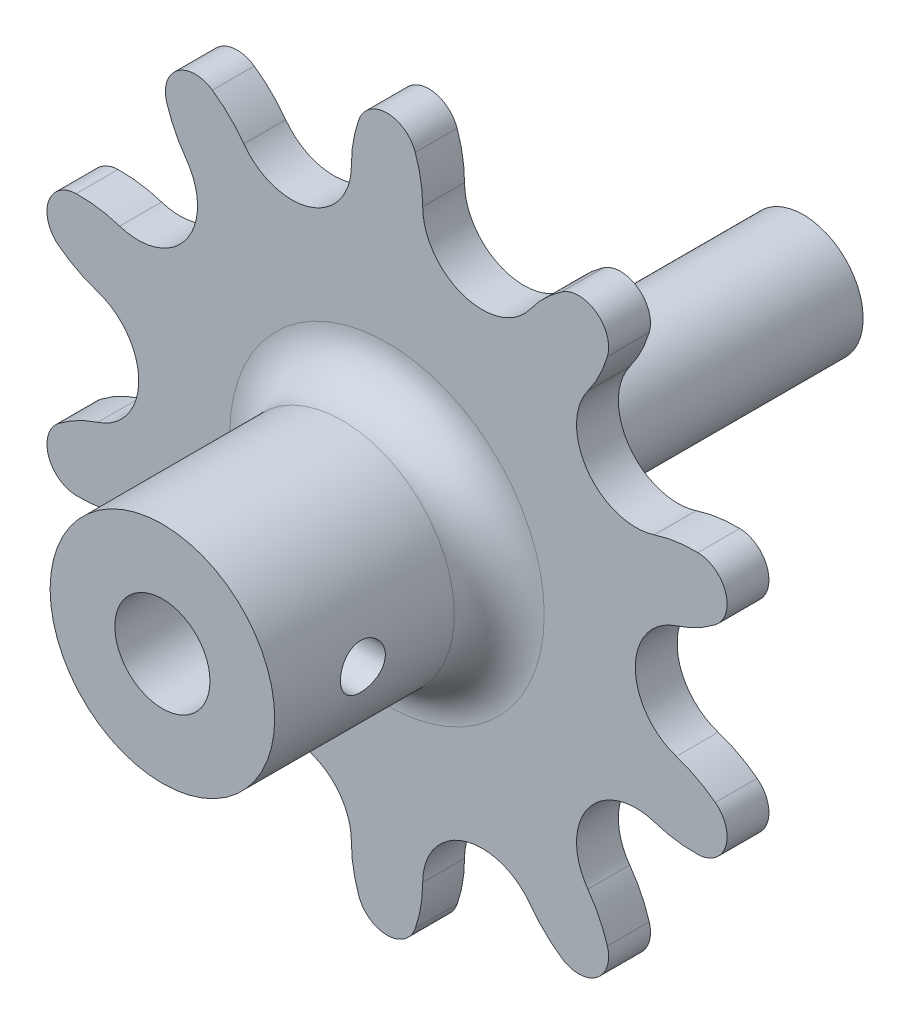
SolidWorks part; units mm, degrees
ref_plane "Front Plane" through (0, 0, 0) normal (0, 0, 1) x (1, 0, 0)
ref_plane "Top Plane" through (0, 0, 0) normal (0, 1, 0) x (1, 0, 0)
ref_plane "Right Plane" through (0, 0, 0) normal (1, 0, 0) x (0, 0, -1)
sketch "Sketch2" plane through (0, 0, 0) normal (0, 0, 1) x (1, 0, 0)
  line L0 (0, 0) -> (-12.7, 0) construction
  line L1 (-6.35, 0) -> (-6.35, -19.5433) construction
  line L2 (-6.35, -19.5433) -> (-12.7, 0) construction
  line L3 (-6.35, -19.5433) -> (0, 0) construction
  line L4 (-6.35, 0) -> (-6.35, 13.4382) construction
  circle A0 centre (0, 0) radius 3.9688 construction
  circle A1 centre (-12.7, 0) radius 3.9688 construction
  arc A2 (-8.7312, 0) -> (-8.2367, 2.8967) centre (0, 0) cw
  arc A3 (-3.9688, 0) -> (-4.4633, 2.8967) centre (-12.7, 0) ccw
  arc A4 (-8.2367, 2.8967) -> (-4.4633, 2.8967) centre (-6.35, 2.2332) cw
  arc A5 (-8.7312, 0) -> (-11.4736, -3.7745) centre (-12.7, 0) cw
  arc A6 (-3.9688, 0) -> (-1.2264, -3.7745) centre (0, 0) ccw
  arc A7 (3.2108, -2.3328) -> (-1.2264, -3.7745) centre (0, 0) cw
  arc A8 (7.0637, -5.1321) -> (7.0637, -9.7976) centre (10.2745, -7.4649) ccw
  arc A9 (7.0637, -5.1321) -> (8.3663, -2.4979) centre (0, 0) ccw
  arc A10 (5.3135, -0.2799) -> (8.3663, -2.4979) centre (6.4499, -1.9257) cw
  arc A11 (3.2108, -2.3328) -> (5.3135, -0.2799) centre (10.2745, -7.4649) cw
  arc A12 (11.5009, -11.2394) -> (7.0637, -9.7976) centre (10.2745, -7.4649) cw
  arc A13 (12.9726, -15.7688) -> (10.2303, -19.5433) centre (14.199, -19.5433) ccw
  arc A14 (12.9726, -15.7688) -> (15.5748, -14.4033) centre (10.2745, -7.4649) ccw
  arc A15 (14.4087, -10.8146) -> (15.5748, -14.4033) centre (14.3607, -12.814) cw
  arc A16 (11.5009, -11.2394) -> (14.4087, -10.8146) centre (14.199, -19.5433) cw
  arc A17 (12.9726, -23.3178) -> (10.2303, -19.5433) centre (14.199, -19.5433) cw
  arc A18 (11.5009, -27.8472) -> (7.0637, -29.2889) centre (10.2745, -31.6217) ccw
  arc A19 (11.5009, -27.8472) -> (14.4087, -28.272) centre (14.199, -19.5433) ccw
  arc A20 (15.5748, -24.6833) -> (14.4087, -28.272) centre (14.3607, -26.2726) cw
  arc A21 (12.9726, -23.3178) -> (15.5748, -24.6833) centre (10.2745, -31.6217) cw
  arc A22 (7.0637, -33.9545) -> (7.0637, -29.2889) centre (10.2745, -31.6217) cw
  arc A23 (3.2108, -36.7538) -> (-1.2264, -35.3121) centre (0, -39.0866) ccw
  arc A24 (3.2108, -36.7538) -> (5.3135, -38.8066) centre (10.2745, -31.6217) ccw
  arc A25 (8.3663, -36.5887) -> (5.3135, -38.8066) centre (6.4499, -37.1608) cw
  arc A26 (7.0637, -33.9545) -> (8.3663, -36.5887) centre (0, -39.0866) cw
  arc A27 (-3.9687, -39.0866) -> (-1.2264, -35.3121) centre (0, -39.0866) cw
  arc A28 (-8.7312, -39.0866) -> (-11.4736, -35.3121) centre (-12.7, -39.0866) ccw
  arc A29 (-8.7312, -39.0866) -> (-8.2367, -41.9833) centre (0, -39.0866) ccw
  arc A30 (-4.4633, -41.9833) -> (-8.2367, -41.9833) centre (-6.35, -41.3198) cw
  arc A31 (-3.9687, -39.0866) -> (-4.4633, -41.9833) centre (-12.7, -39.0866) cw
  arc A32 (-15.9108, -36.7538) -> (-11.4736, -35.3121) centre (-12.7, -39.0866) cw
  arc A33 (-19.7637, -33.9545) -> (-19.7637, -29.2889) centre (-22.9745, -31.6217) ccw
  arc A34 (-19.7637, -33.9545) -> (-21.0663, -36.5887) centre (-12.7, -39.0866) ccw
  arc A35 (-18.0135, -38.8066) -> (-21.0663, -36.5887) centre (-19.1499, -37.1608) cw
  arc A36 (-15.9108, -36.7538) -> (-18.0135, -38.8066) centre (-22.9745, -31.6217) cw
  arc A37 (-24.2009, -27.8472) -> (-19.7637, -29.2889) centre (-22.9745, -31.6217) cw
  arc A38 (-25.6726, -23.3178) -> (-22.9303, -19.5433) centre (-26.899, -19.5433) ccw
  arc A39 (-25.6726, -23.3178) -> (-28.2748, -24.6833) centre (-22.9745, -31.6217) ccw
  arc A40 (-27.1087, -28.272) -> (-28.2748, -24.6833) centre (-27.0607, -26.2726) cw
  arc A41 (-24.2009, -27.8472) -> (-27.1087, -28.272) centre (-26.899, -19.5433) cw
  arc A42 (-25.6726, -15.7688) -> (-22.9303, -19.5433) centre (-26.899, -19.5433) cw
  arc A43 (-24.2009, -11.2394) -> (-19.7637, -9.7976) centre (-22.9745, -7.4649) ccw
  arc A44 (-24.2009, -11.2394) -> (-27.1087, -10.8146) centre (-26.899, -19.5433) ccw
  arc A45 (-28.2748, -14.4033) -> (-27.1087, -10.8146) centre (-27.0607, -12.814) cw
  arc A46 (-25.6726, -15.7688) -> (-28.2748, -14.4033) centre (-22.9745, -7.4649) cw
  arc A47 (-19.7637, -5.1321) -> (-19.7637, -9.7976) centre (-22.9745, -7.4649) cw
  arc A48 (-15.9108, -2.3328) -> (-11.4736, -3.7745) centre (-12.7, 0) ccw
  arc A49 (-15.9108, -2.3328) -> (-18.0135, -0.2799) centre (-22.9745, -7.4649) ccw
  arc A50 (-21.0663, -2.4979) -> (-18.0135, -0.2799) centre (-19.1499, -1.9257) cw
  arc A51 (-19.7637, -5.1321) -> (-21.0663, -2.4979) centre (-12.7, 0) cw
  dimension "D1" = 7.9375
  dimension "D4" = 2
  dimension "D2" = 12.7
  dimension "D3" = 36
  dimension "D5" = 10
extrude "Boss-Extrude1" add sketch "Sketch2" along normal blind 2.794
sketch "Sketch3" plane through (0, 0, 2.794) normal (0, 0, 1) x (1, 0, 0)
  circle A0 centre (-6.35, -19.5433) radius 7.5
  circle A1 centre (-6.35, -19.5433) radius 3.175
  dimension "D1" = 15
  dimension "D2" = 6.35
extrude "Boss-Extrude2" add sketch "Sketch3" along normal blind 15
fillet "Fillet1" radius 3 1 edges at (-13.85, -19.5433, 2.794)
sketch "Sketch4" plane through (0, 0, 0) normal (1, 0, 0) x (0, 0, -1)
  line L0 (-17.794, -19.5433) -> (0, -19.5433) construction
  line L1 (-17.794, -12.0433) -> (-17.794, -27.0433) construction
  line L2 (0, -15.7688) -> (0, -19.5433) construction
  circle A0 centre (-11.9061, -19.5433) radius 1.5
  dimension "D1" = 3
extrude "Cut-Extrude1" cut sketch "Sketch4" against normal mid plane 15
sketch "Sketch5" plane through (0, 0, 0) normal (0, 0, -1) x (-1, 0, 0)
  circle A0 centre (6.35, -19.5433) radius 4
  dimension "D1" = 8
extrude "Boss-Extrude3" add sketch "Sketch5" along normal blind 25
